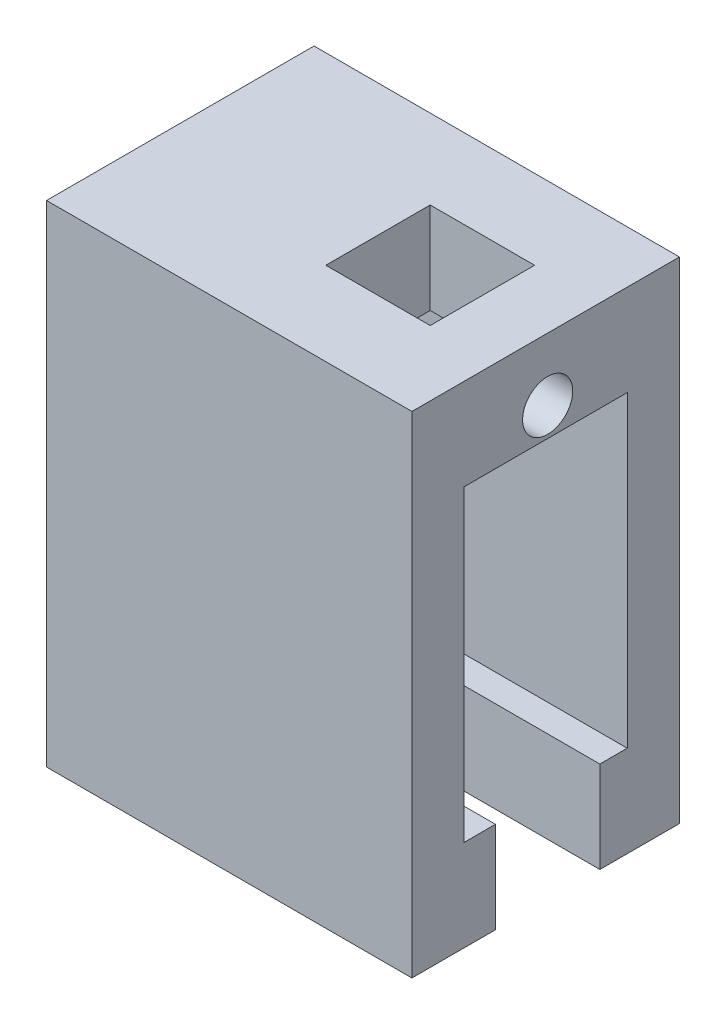
SolidWorks part; units mm, degrees
ref_plane "Front Plane" through (0, 0, 0) normal (0, 0, 1) x (1, 0, 0)
ref_plane "Top Plane" through (0, 0, 0) normal (0, 1, 0) x (1, 0, 0)
ref_plane "Right Plane" through (0, 0, 0) normal (1, 0, 0) x (0, 0, -1)
sketch "Sketch1" plane through (0, 0, 0) normal (1, 0, 0) x (0, 0, -1)
  line L1 (-10.4, -19.35) -> (10.1, -19.35)
  line L2 (-10.4, -19.35) -> (-10.4, 18.25)
  line L3 (-10.4, 18.25) -> (10.1, 18.25)
  line L4 (10.1, -19.35) -> (10.1, 18.25)
  line L7 (-6.4, -12.35) -> (6.1, -12.35)
  line L8 (-6.4, -12.35) -> (-6.4, 11.25)
  line L9 (-6.4, 11.25) -> (6.1, 11.25)
  line L10 (6.1, -12.35) -> (6.1, 11.25)
  line L11 (-6.4, -12.35) -> (6.1, 11.25) construction
  line L12 (-6.4, 11.25) -> (6.1, -12.35) construction
  point P0 (0, 0)
  point P6 (-0.15, -0.55)
  dimension "D1" = 12.5
  dimension "D2" = 23.6
  dimension "D3" = 4
  dimension "D4" = 7
  dimension "D5" = 7
  dimension "D6" = 4
extrude "Boss-Extrude1" add sketch "Sketch1" along normal blind 28
sketch "Sketch2" plane through (28, 0, 0) normal (1, 0, 0) x (0, 0, -1)
  line L0 (6.1, 11.25) -> (-6.4, 11.25) construction
  circle A0 centre (0, 13.45) radius 1.92
  dimension "D1" = 3.84
  dimension "D2" = 2.2
extrude "Cut-Extrude1" cut sketch "Sketch2" against normal blind 13
sketch "Sketch3" plane through (15, 0, 0) normal (1, 0, 0) x (0, 0, -1)
  line L0 (6.1, 11.25) -> (-6.4, 11.25) construction
  line L5 (-4, 11.25) -> (-4, 18.25)
  line L6 (-4, 18.25) -> (4, 18.25)
  line L11 (-4, 11.25) -> (4, 11.25)
  line L12 (0, 20.011) -> (0, -20.812) construction
  line L13 (4, 11.25) -> (4, 18.25)
  point P13 (0, 11.25)
  point P14 (0, 18.25)
  dimension "D3" = 7
  dimension "D4" = 8
extrude "Cut-Extrude2" cut sketch "Sketch3" along normal blind 8
sketch "Sketch4" plane through (28, 0, 0) normal (1, 0, 0) x (0, 0, -1)
  line L0 (0, -7.6507) -> (0, -19.6626) construction
  line L1 (4, -12.35) -> (-4, -12.35)
  line L2 (-6.4, -12.35) -> (6.1, -12.35) construction
  line L3 (-4, -12.35) -> (-4, -19.35)
  line L4 (-10.4, -19.35) -> (10.1, -19.35) construction
  line L5 (-4, -19.35) -> (4, -19.35)
  line L6 (4, -12.35) -> (4, -19.35)
  point P12 (0, -19.35)
  point P13 (0, -12.35)
  dimension "D1" = 8
extrude "Cut-Extrude3" cut sketch "Sketch4" against normal blind 20
